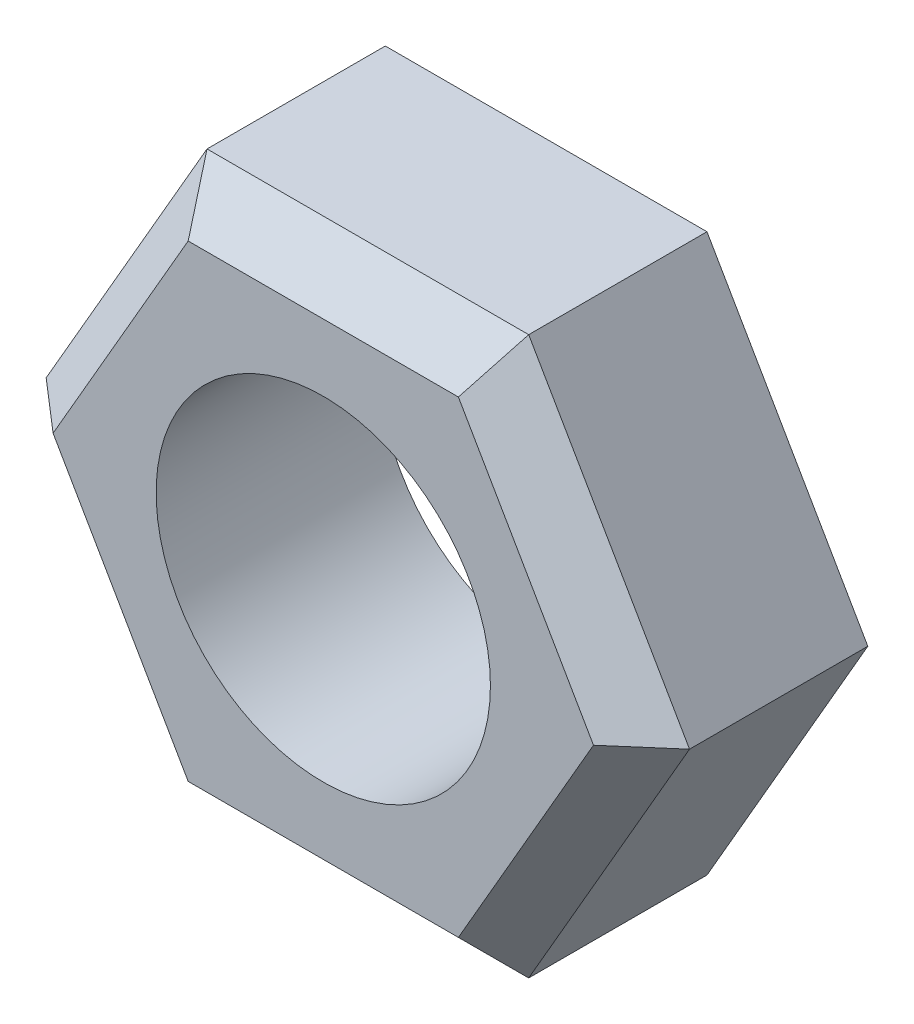
SolidWorks part; units mm, degrees
ref_plane "Front Plane" through (0, 0, 0) normal (0, 0, 1) x (1, 0, 0)
ref_plane "Top Plane" through (0, 0, 0) normal (0, 1, 0) x (1, 0, 0)
ref_plane "Right Plane" through (0, 0, 0) normal (1, 0, 0) x (0, 0, -1)
sketch "Sketch1" plane through (0, 0, 0) normal (0, 0, 1) x (1, 0, 0)
  line L1 (7.2169, -12.5) -> (14.4338, 0)
  line L2 (14.4338, 0) -> (7.2169, 12.5)
  line L3 (7.2169, 12.5) -> (-7.2169, 12.5)
  line L4 (-7.2169, 12.5) -> (-14.4338, 0)
  line L5 (-14.4338, 0) -> (-7.2169, -12.5)
  line L6 (-7.2169, -12.5) -> (7.2169, -12.5)
  circle A0 centre (0, 0) radius 12.5 construction
  circle A1 centre (0, 0) radius 7.5
  dimension "D1" = 25
  dimension "D2" = 15
extrude "Boss-Extrude1" add sketch "Sketch1" along normal blind 10
chamfer "Chamfer1" distance 2 angle 45 6 edges at (-10.8253, -6.25, 10) (0, -12.5, 10) (10.8253, -6.25, 10) (10.8253, 6.25, 10) (-10.8253, 6.25, 10) (0, 12.5, 10)
